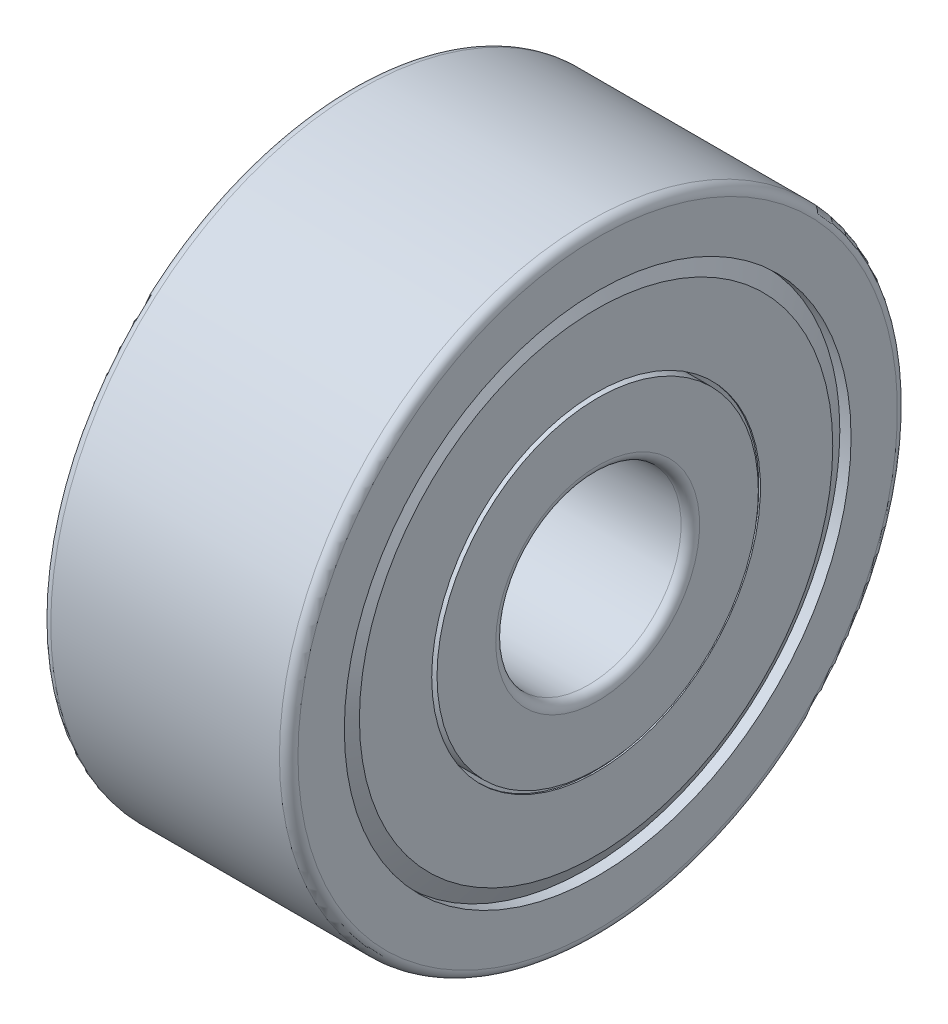
SolidWorks part; units mm, degrees
ref_plane "Plan de face" through (0, 0, 0) normal (0, 0, 1) x (1, 0, 0)
ref_plane "Plan de dessus" through (0, 0, 0) normal (0, 1, 0) x (1, 0, 0)
ref_plane "Plan de droite" through (0, 0, 0) normal (1, 0, 0) x (0, 0, -1)
ref_plane "Plan1" through (0, 0, 0) normal (0, 0, -1) x (-1, 0, 0)
sketch "Esquisse1" plane through (0, 0, 0) normal (0, 0, -1) x (-1, 0, 0)
  line L0 (-4, 2.6) -> (-4, 1.65)
  line L1 (-3.85, 1.5) -> (-0.15, 1.5)
  line L2 (0, 1.65) -> (0, 2.6)
  line L3 (0, 2.6) -> (-0.8875, 2.6)
  line L4 (-0.755, 3.85) -> (-0.3636, 3.85)
  line L5 (-0.3636, 3.85) -> (-0.3636, 4.1)
  line L6 (-0.259, 4.1899) -> (-0.2618, 4.1882)
  line L7 (-0.2618, 4.1882) -> (-0.051, 3.8231)
  line L8 (-0.051, 3.8231) -> (-0.051, 2.66)
  line L9 (-0.051, 2.66) -> (-0.026, 2.66)
  line L10 (-0.026, 2.66) -> (-0.026, 3.8298)
  line L11 (-0.026, 3.8298) -> (-0.2276, 4.1789)
  line L12 (-0.1818, 4.1) -> (0, 4.1)
  line L13 (0, 4.1) -> (0, 4.85)
  line L14 (-0.15, 5) -> (-3.85, 5)
  line L15 (-4, 4.85) -> (-4, 4.1)
  line L16 (-4, 4.1) -> (-3.8182, 4.1)
  line L17 (-3.7724, 4.1789) -> (-3.974, 3.8298)
  line L18 (-3.974, 3.8298) -> (-3.974, 2.66)
  line L19 (-3.974, 2.66) -> (-3.949, 2.66)
  line L20 (-3.949, 2.66) -> (-3.949, 3.8231)
  line L21 (-3.949, 3.8231) -> (-3.7382, 4.1882)
  line L22 (-3.7382, 4.1882) -> (-3.741, 4.1899)
  line L23 (-3.6364, 4.1) -> (-3.6364, 3.85)
  line L24 (-3.6364, 3.85) -> (-3.245, 3.85)
  line L25 (-3.1125, 2.6) -> (-4, 2.6)
  line L26 (-4, 0) -> (0, 0) construction
  arc A0 (-4, 1.65) -> (-3.85, 1.5) centre (-3.85, 1.65) ccw
  arc A1 (-0.15, 1.5) -> (0, 1.65) centre (-0.15, 1.65) ccw
  arc A2 (-0.8875, 2.6) -> (-0.755, 3.85) centre (-2, 3.35) ccw
  arc A3 (-0.3636, 4.1) -> (-0.259, 4.1899) centre (-0.2727, 4.1) cw
  arc A4 (-0.2276, 4.1789) -> (-0.1818, 4.1) centre (-0.2727, 4.1) cw
  arc A5 (0, 4.85) -> (-0.15, 5) centre (-0.15, 4.85) ccw
  arc A6 (-3.85, 5) -> (-4, 4.85) centre (-3.85, 4.85) ccw
  arc A7 (-3.8182, 4.1) -> (-3.7724, 4.1789) centre (-3.7273, 4.1) cw
  arc A8 (-3.741, 4.1899) -> (-3.6364, 4.1) centre (-3.7273, 4.1) cw
  arc A9 (-3.245, 3.85) -> (-3.1125, 2.6) centre (-2, 3.35) ccw
  dimension "D2" = 0.15
  dimension "D3" = 1.3417
  dimension "D4" = 0.0909
  dimension "D5" = 0.0909
  dimension "D6" = 0.026
  dimension "D7" = 0.051
  dimension "D8" = 0.0909
  dimension "D9" = 0.0909
  dimension "D10" = 1.3417
  dimension "D11" = 0.1818
  dimension "D12" = 0.2276
  dimension "D13" = 0.259
  dimension "D14" = 0.2618
  dimension "D15" = 0.755
  dimension "D16" = 0.8875
  dimension "D17" = 2
  dimension "D18" = 3.6364
  dimension "D19" = 1.5
  dimension "D20" = 2.6
  dimension "D21" = 2.66
  dimension "D22" = 4.1
  dimension "D23" = 3.8231
  dimension "D24" = 3.7382
  dimension "D25" = 3.8298
  dimension "D28" = 3.949
  dimension "D29" = 3.974
  dimension "D30" = 4
  dimension "D32" = 4.1882
  dimension "D34" = 5
revolve "Révolution1" add sketch "Esquisse1" angle 360 about L26
